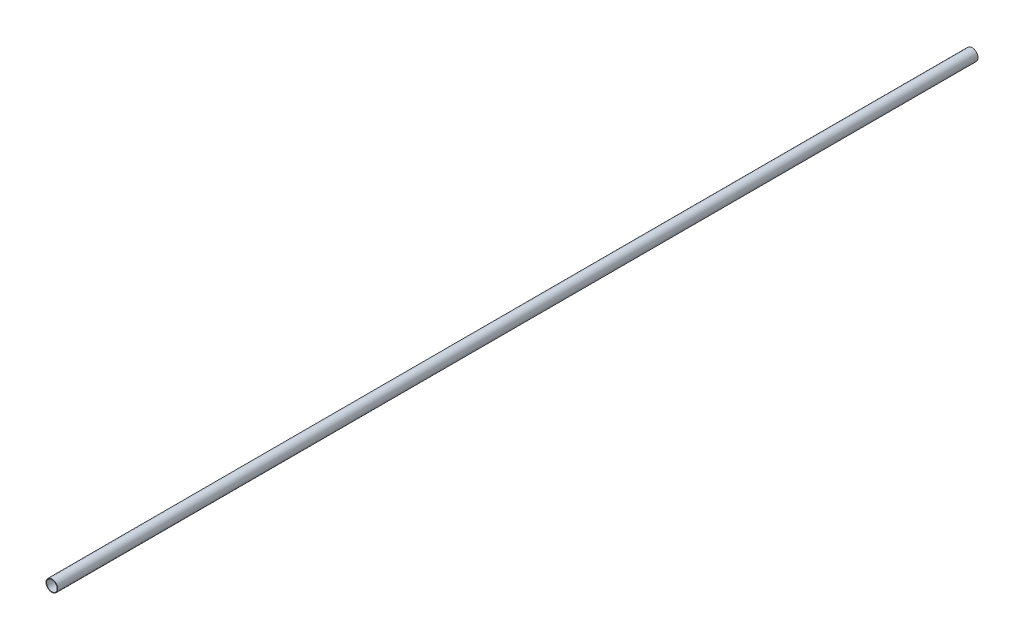
SolidWorks part; units mm, degrees
material "carbon fiber"
ref_plane "Front Plane" through (0, 0, 0) normal (0, 0, 1) x (1, 0, 0)
ref_plane "Top Plane" through (0, 0, 0) normal (0, 1, 0) x (1, 0, 0)
ref_plane "Right Plane" through (0, 0, 0) normal (1, 0, 0) x (0, 0, -1)
sketch "Эскиз1" plane through (0, 0, 0) normal (0, 0, 1) x (1, 0, 0)
  circle A0 centre (0, 0) radius 5
  circle A1 centre (0, 0) radius 4.5
  dimension "D1" = 10
  dimension "D2" = 0.5
extrude "Бобышка-Вытянуть1" add sketch "Эскиз1" along normal mid plane 784
